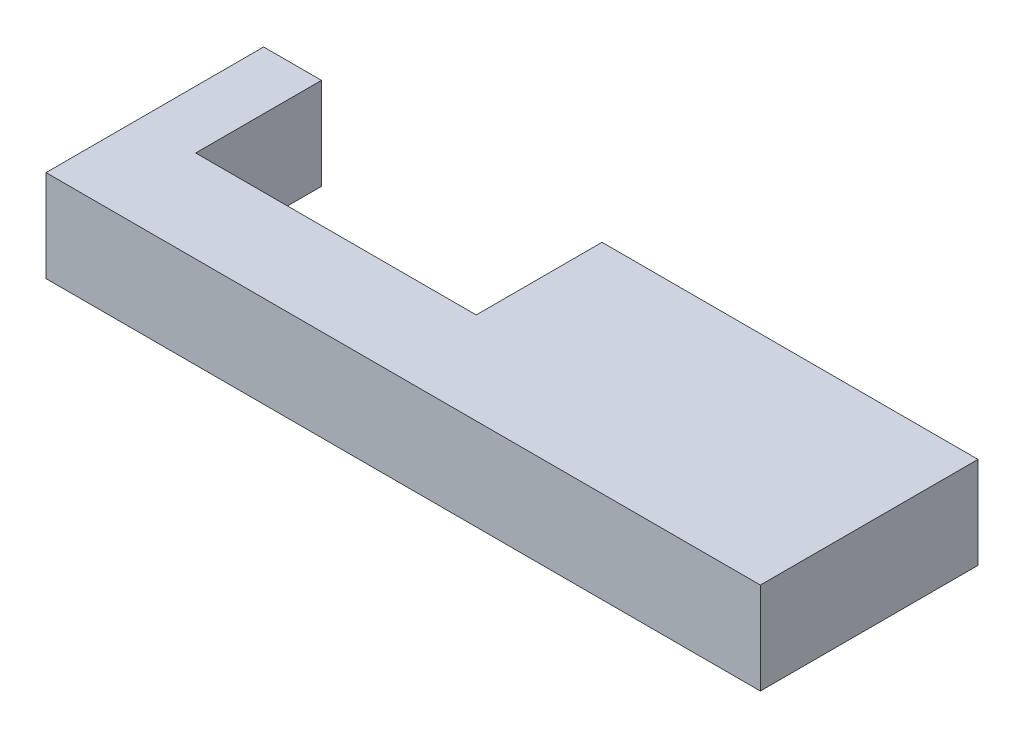
SolidWorks part; units mm, degrees
ref_plane "Front Plane" through (0, 0, 0) normal (0, 0, 1) x (1, 0, 0)
ref_plane "Top Plane" through (0, 0, 0) normal (0, 1, 0) x (1, 0, 0)
ref_plane "Right Plane" through (0, 0, 0) normal (1, 0, 0) x (0, 0, -1)
sketch "Sketch1" plane through (0, 0, 0) normal (0, 1, 0) x (1, 0, 0)
  line L0 (0, 0) -> (19.4, 0)
  line L1 (0, 0) -> (0, 8.7)
  line L2 (19.4, 0) -> (19.4, 8.7)
  line L3 (19.4, 8.7) -> (23.4, 8.7)
  line L4 (23.4, 8.7) -> (23.4, -6.35)
  line L5 (23.4, -6.35) -> (-4, -6.35)
  line L6 (9.7, 0) -> (9.7, 7.262) construction
  line L7 (-4, 8.7) -> (-4, -6.35)
  line L8 (0, 8.7) -> (-4, 8.7)
  point P11 (9.7, -6.35)
  dimension "D1" = 19.4
  dimension "D2" = 4
  dimension "D4" = 6.35
  dimension "D5" = 8.7
extrude "Boss-Extrude1" add sketch "Sketch1" along normal blind 6.35
ref_plane "Plane1" through (23.4, 0, 6.35) normal (0, 0, -1) x (-1, 0, 0)
ref_plane "Plane2" through (23.4, 0, 0) normal (1, 0, 0) x (0, 0, -1)
sketch "Sketch3" plane through (23.4, 0, 0) normal (1, 0, 0) x (0, 0, -1)
  line L1 (8.7, 6.35) -> (-6.35, 6.35)
  line L2 (8.7, 6.35) -> (8.7, 0)
  line L3 (8.7, 0) -> (-6.35, 0)
  line L4 (-6.35, 6.35) -> (-6.35, 0)
extrude "Boss-Extrude2" add sketch "Sketch3" along normal blind 22
